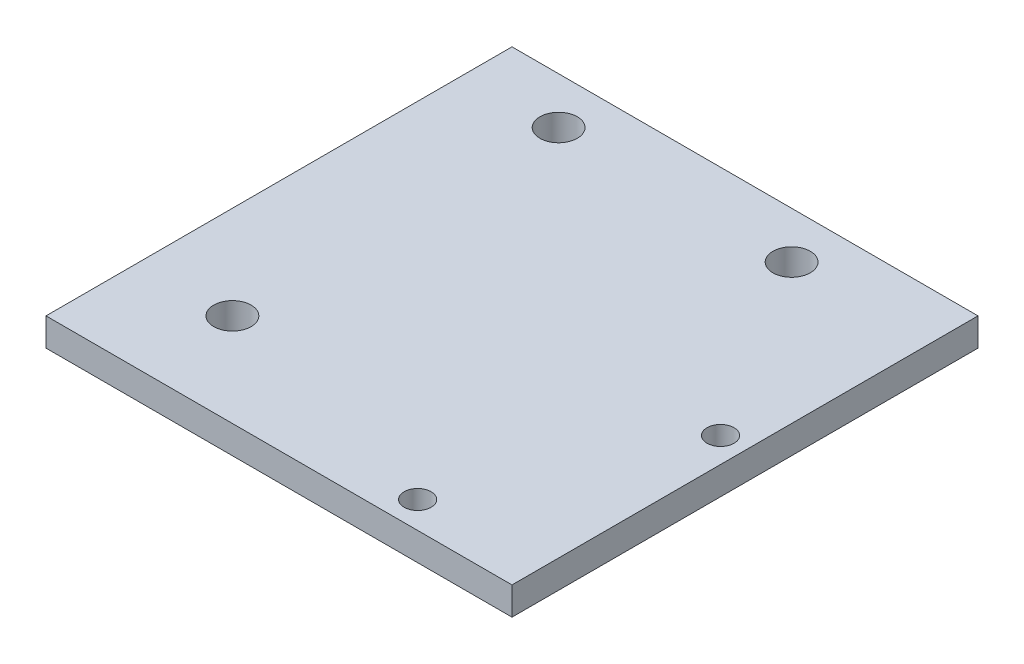
SolidWorks part; units mm, degrees
material "Acrylic (Medium-high impact)"
ref_plane "Front Plane" through (0, 0, 0) normal (0, 0, 1) x (1, 0, 0)
ref_plane "Top Plane" through (0, 0, 0) normal (0, 1, 0) x (1, 0, 0)
ref_plane "Right Plane" through (0, 0, 0) normal (1, 0, 0) x (0, 0, -1)
sketch "Sketch1" plane through (0, 0, 0) normal (0, 1, 0) x (1, 0, 0)
  line L1 (0, 0) -> (50, 0)
  line L2 (0, 0) -> (0, 50)
  line L3 (0, 50) -> (50, 50)
  line L4 (50, 0) -> (50, 50)
  dimension "D1" = 50
extrude "Boss-Extrude1" add sketch "Sketch1" along normal blind 3
sketch "Sketch2" plane through (0, 3, 0) normal (0, 1, 0) x (1, 0, 0)
  line L1 (35, 45) -> (10, 45) construction
  line L2 (50, 50) -> (0, 50) construction
  line L18 (0, 0) -> (50, 0) construction
  line L19 (0, 50) -> (0, 0) construction
  circle A0 centre (10, 45) radius 2.0066
  circle A1 centre (35, 45) radius 2.0066
  circle A5 centre (10, 10) radius 2.0066
  dimension "D2" = 5
  dimension "D3" = 10
  dimension "D4" = 25
  dimension "D10" = 4.0132
  dimension "D5" = 10
  dimension "D6" = 10
extrude "Cut-Extrude1" cut sketch "Sketch2" against normal through all
sketch "Sketch3" plane through (0, 3, 0) normal (0, 1, 0) x (1, 0, 0)
  circle A0 centre (47.3017, 25.0739) radius 1.45
  circle A1 centre (37.0017, 2.8739) radius 1.45
  dimension "D1" = 2.9
extrude "Cut-Extrude2" cut sketch "Sketch3" against normal up to next
